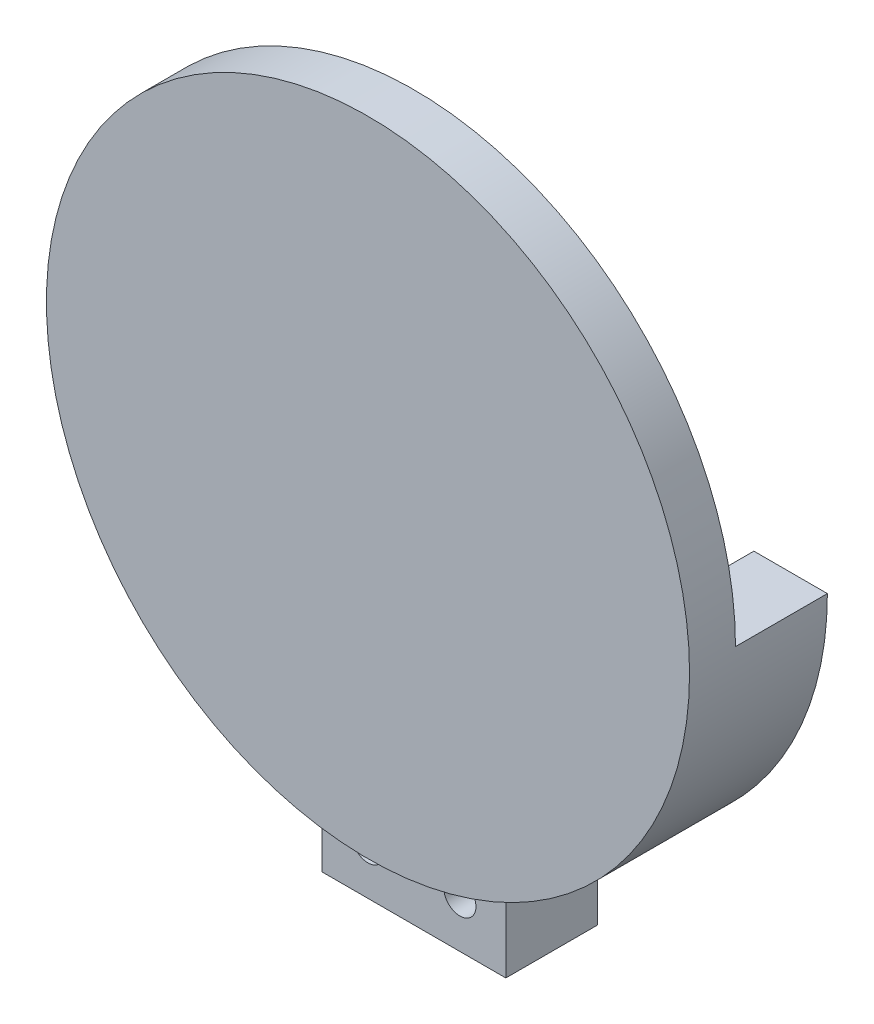
SolidWorks part; units mm, degrees
ref_plane "Front Plane" through (0, 0, 0) normal (0, 0, 1) x (1, 0, 0)
ref_plane "Top Plane" through (0, 0, 0) normal (0, 1, 0) x (1, 0, 0)
ref_plane "Right Plane" through (0, 0, 0) normal (1, 0, 0) x (0, 0, -1)
sketch "Sketch1" plane through (0, 0, 0) normal (0, 0, 1) x (1, 0, 0)
  circle A0 centre (0, 0) radius 4.1
  dimension "D1" = 8.2
extrude "Boss-Extrude1" add sketch "Sketch1" along normal blind 7
sketch "Sketch2" plane through (0, 0, 7) normal (0, 0, 1) x (1, 0, 0)
  circle A0 centre (0, 0) radius 6.25
  dimension "D1" = 12.5
extrude "Boss-Extrude2" add sketch "Sketch2" along normal blind 2
sketch "Sketch3" plane through (0, 0, 9) normal (0, 0, 1) x (1, 0, 0)
  circle A0 centre (0, 0) radius 35
  dimension "D1" = 70
extrude "Boss-Extrude3" add sketch "Sketch3" along normal blind 5
sketch "Sketch4" plane through (0, 0, 14) normal (0, 0, 1) x (1, 0, 0)
  circle A0 centre (0, 0) radius 25
  dimension "D1" = 50
extrude "Boss-Extrude4" add sketch "Sketch4" along normal blind 5
sketch "Sketch5" plane through (0, 0, 19) normal (0, 0, 1) x (1, 0, 0)
  circle A0 centre (0, 0) radius 30
extrude "Boss-Extrude5" add sketch "Sketch5" along normal blind 2
fillet "Fillet1" radius 2 1 edges at (25, 0, 19)
fillet "Fillet2" radius 2 1 edges at (25, 0, 14)
sketch "Sketch6" plane through (0, 0, 0) normal (0, 1, 0) x (1, 0, 0)
  line L0 (0, 0) -> (0, -39.6093) construction
  line L1 (25, -16) -> (-25, -16) construction
  line L2 (0, -16) -> (-30.3763, -16) construction
  line L3 (2.9572, -17) -> (-29.7434, -17) construction
  line L4 (25, -17) -> (-25, -17) construction
  line L5 (0.5721, -17) -> (-0.5375, -17) construction
  line L6 (0.0173, -17) -> (0, -16) construction
  circle A0 centre (0.0086, -16.5) radius 1.5
  dimension "D1" = 3
extrude "Cut-Extrude1" cut sketch "Sketch6" against normal through all both and the other way through all contours A0
sketch "Sketch7" plane through (0, 0, 9) normal (0, 0, -1) x (-1, 0, 0)
  line L1 (10, -33.541) -> (10, -33.7353)
  line L2 (10, -33.541) -> (10, -66.6674) construction
  line L3 (10, -33.7353) -> (10, -43.7353)
  line L4 (0, 0) -> (0, -15.6299) construction
  line L5 (-10, -33.541) -> (-10, -66.6674) construction
  line L6 (-10, -33.7353) -> (-10, -43.7353)
  line L7 (-10, -33.541) -> (-10, -33.7353)
  line L8 (-10, -43.7353) -> (10, -43.7353)
  line L9 (-35, 0) -> (-27, 0)
  line L10 (10, -33.541) -> (10, -25.0799)
  arc A0 (-27, 0) -> (10, -25.0799) centre (0, 0) ccw
  arc A1 (-10, -33.541) -> (-35, 0) centre (0, 0) cw
  point P16 (0, -43.7353)
  dimension "D3" = 10
extrude "Boss-Extrude6" add sketch "Sketch7" along normal blind 10
sketch "Sketch9" plane through (0, 0, -1) normal (0, 0, -1) x (-1, 0, 0)
  line L0 (0, 0) -> (0, -70.6558) construction
  line L2 (10, -33.541) -> (0, -43.7353) construction
  line L3 (-10, -43.7353) -> (10, -43.7353) construction
  line L4 (0, -43.7353) -> (-10, -33.541) construction
  circle A0 centre (5, -38.6382) radius 1.75
  circle A1 centre (-5, -38.6382) radius 1.75
  dimension "D1" = 3.5
extrude "Cut-Extrude2" cut sketch "Sketch9" against normal blind 10
sketch "Sketch10" plane through (0, 0, 14) normal (0, 0, 1) x (1, 0, 0)
  circle A0 centre (0, 0) radius 52.5097
extrude "Cut-Extrude3" cut sketch "Sketch10" along normal blind 40
